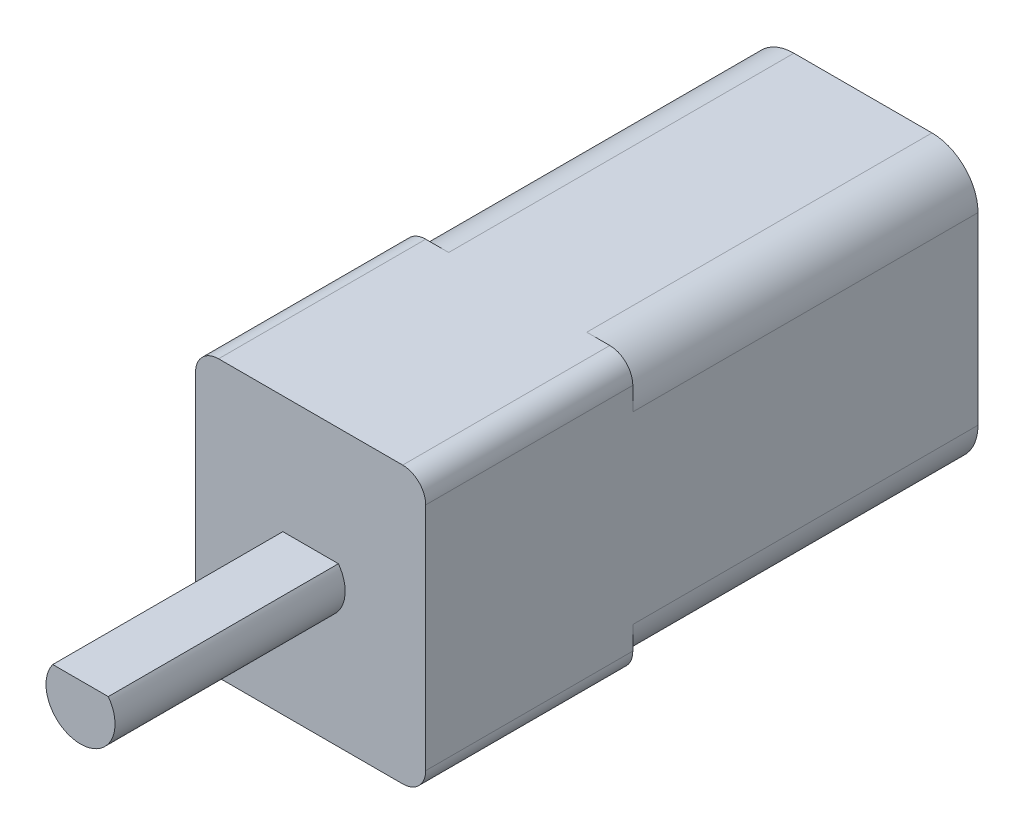
SolidWorks part; units mm, degrees
ref_plane "Front Plane" through (0, 0, 0) normal (0, 0, 1) x (1, 0, 0)
ref_plane "Top Plane" through (0, 0, 0) normal (0, 1, 0) x (1, 0, 0)
ref_plane "Right Plane" through (0, 0, 0) normal (1, 0, 0) x (0, 0, -1)
sketch "Sketch1" plane through (0, 0, 0) normal (0, 0, 1) x (1, 0, 0)
  line L1 (2, 0) -> (8, 0)
  line L2 (0, 2) -> (0, 10)
  line L3 (2, 12) -> (8, 12)
  line L4 (10, 2) -> (10, 10)
  arc A0 (2, 0) -> (0, 2) centre (2, 2) cw
  arc A1 (8, 0) -> (10, 2) centre (8, 2) ccw
  arc A2 (10, 10) -> (8, 12) centre (8, 10) ccw
  arc A3 (0, 10) -> (2, 12) centre (2, 10) cw
  point P7 (0, 0)
  point P12 (10, 12)
  point P15 (0, 12)
  dimension "D3" = 2
  dimension "D1" = 12
  dimension "D2" = 10
extrude "Boss-Extrude1" add sketch "Sketch1" along normal blind 15
sketch "Sketch2" plane through (0, 0, 15) normal (0, 0, 1) x (1, 0, 0)
  line L1 (1, 0) -> (9, 0)
  line L2 (0, 1) -> (0, 11)
  line L3 (1, 12) -> (9, 12)
  line L4 (10, 1) -> (10, 11)
  arc A0 (1, 0) -> (0, 1) centre (1, 1) cw
  arc A1 (10, 1) -> (9, 0) centre (9, 1) cw
  arc A2 (10, 11) -> (9, 12) centre (9, 11) ccw
  arc A3 (0, 11) -> (1, 12) centre (1, 11) cw
  point P7 (0, 0)
  point P10 (10, 0)
  point P13 (10, 12)
  point P16 (0, 12)
  dimension "D3" = 1
  dimension "D1" = 10
  dimension "D2" = 12
extrude "Boss-Extrude2" add sketch "Sketch2" along normal blind 9
sketch "Sketch3" plane through (0, 0, 24) normal (0, 0, 1) x (1, 0, 0)
  line L0 (1, 0) -> (9, 0) construction
  line L1 (10, 1) -> (10, 11) construction
  line L2 (0, 11) -> (0, 1) construction
  line L3 (9, 12) -> (1, 12) construction
  line L4 (1, 0) -> (9, 0)
  line L5 (10, 1) -> (10, 11)
  line L6 (0, 11) -> (0, 1)
  line L7 (9, 12) -> (1, 12)
  line L8 (3.7933, 6.891) -> (6.2067, 6.891)
  circle A0 centre (5, 6) radius 1.5
  arc A1 (0, 1) -> (1, 0) centre (1, 1) ccw construction
  arc A2 (9, 0) -> (10, 1) centre (9, 1) ccw construction
  arc A3 (10, 11) -> (9, 12) centre (9, 11) ccw construction
  arc A4 (1, 12) -> (0, 11) centre (1, 11) ccw construction
  arc A5 (0, 1) -> (1, 0) centre (1, 1) ccw
  arc A6 (9, 0) -> (10, 1) centre (9, 1) ccw
  arc A7 (10, 11) -> (9, 12) centre (9, 11) ccw
  arc A8 (1, 12) -> (0, 11) centre (1, 11) ccw
  dimension "D2" = 6
  dimension "D3" = 3
  dimension "D1" = 5
extrude "Boss-Extrude3" add sketch "Sketch3" along normal blind 10 contours A0
